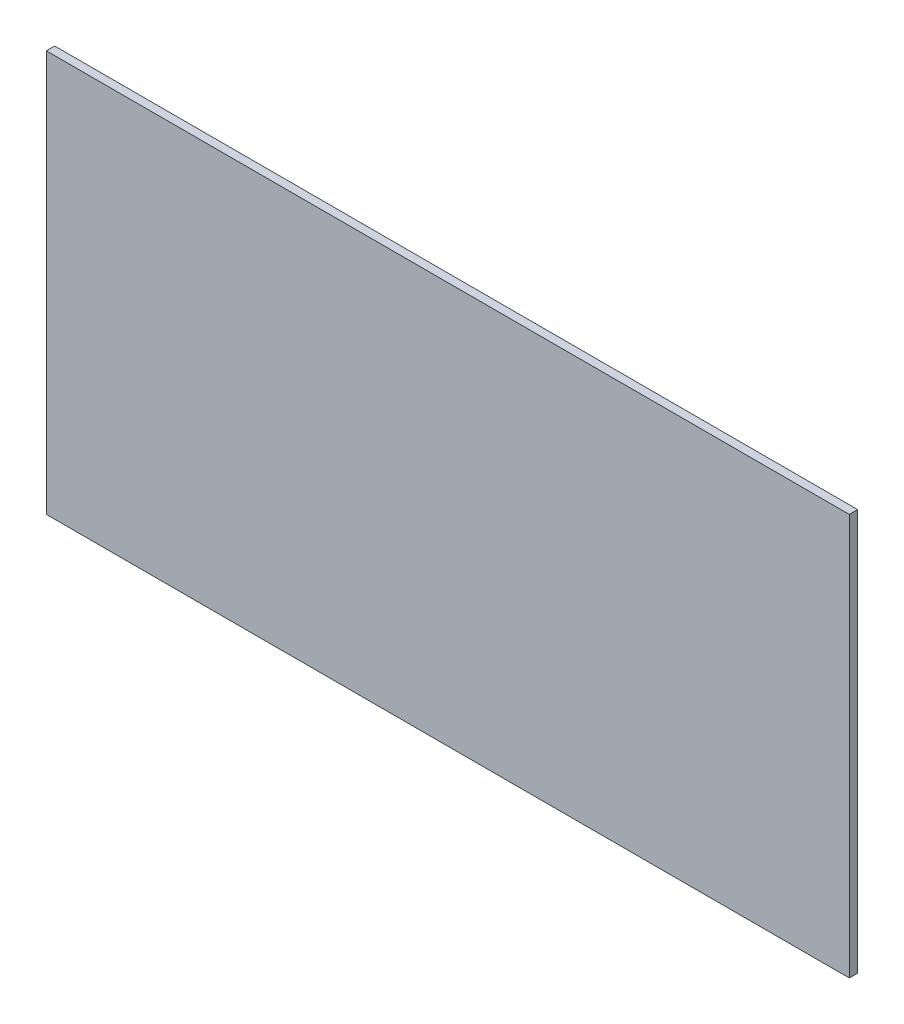
SolidWorks part; units mm, degrees
ref_plane "Front Plane" through (0, 0, 0) normal (0, 0, 1) x (1, 0, 0)
ref_plane "Top Plane" through (0, 0, 0) normal (0, 1, 0) x (1, 0, 0)
ref_plane "Right Plane" through (0, 0, 0) normal (1, 0, 0) x (0, 0, -1)
sketch "Sketch1" plane through (0, 0, 0) normal (0, 0, 1) x (1, 0, 0)
  line L1 (-304.8, -152.4) -> (304.8, -152.4)
  line L2 (-304.8, -152.4) -> (-304.8, 152.4)
  line L3 (-304.8, 152.4) -> (304.8, 152.4)
  line L4 (304.8, -152.4) -> (304.8, 152.4)
  line L5 (-304.8, -152.4) -> (304.8, 152.4) construction
  line L6 (-304.8, 152.4) -> (304.8, -152.4) construction
  point P0 (0, 0)
  point P6 (0, 0)
  dimension "D1" = 304.8
  dimension "D2" = 609.6
extrude "Boss-Extrude1" add sketch "Sketch1" along normal blind 6.35
sketch "Sketch2" plane through (0, 0, 6.35) normal (0, 0, 1) x (1, 0, 0)
  line L0 (0, 0) -> (0, 152.4) construction
  line L1 (304.8, 152.4) -> (-304.8, 152.4) construction
  line L2 (0, 152.4) -> (304.8, 0) construction
  line L3 (304.8, -152.4) -> (304.8, 152.4) construction
  line L5 (-244.65, 149.4) -> (-244.65, 152.4) construction
  line L6 (-301.8, 92.25) -> (-304.8, 92.25) construction
  line L7 (-304.8, 152.4) -> (-304.8, -152.4) construction
  circle A0 centre (-244.65, 92.25) radius 57.15
  circle A11 centre (-82.09, 92.25) radius 57.15
  circle A12 centre (80.47, 92.25) radius 57.15
  circle A13 centre (243.03, 92.25) radius 57.15
  circle A14 centre (-82.09, -91.9) radius 57.15
  circle A15 centre (80.47, -91.9) radius 57.15
  circle A16 centre (243.03, -91.9) radius 57.15
  circle A17 centre (-244.65, -91.9) radius 57.15
  circle A18 centre (-162.8709, 0) radius 57.15
  circle A19 centre (0, 0) radius 57.15
  circle A20 centre (161.9446, 0) radius 57.15
  point P18 (-162.8709, 0)
  point P35 (-4.1592, 0)
  point P37 (161.9446, 0)
  dimension "D1" = 114.3
  dimension "D2" = 3
  dimension "D3" = 4
  dimension "D4" = 2
